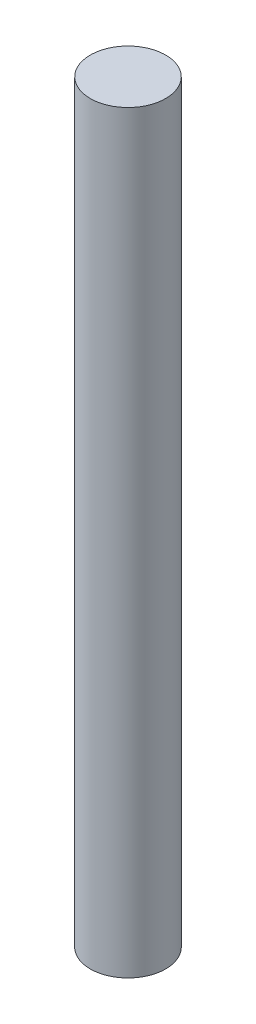
SolidWorks part; units mm, degrees
ref_plane "Plano frontal" through (0, 0, 0) normal (0, 0, 1) x (1, 0, 0)
ref_plane "Plano superior" through (0, 0, 0) normal (0, 1, 0) x (1, 0, 0)
ref_plane "Plano direito" through (0, 0, 0) normal (1, 0, 0) x (0, 0, -1)
sketch "Esboço1" plane through (0, 0, 0) normal (0, 1, 0) x (1, 0, 0)
  circle A0 centre (0, 0) radius 10
extrude "Ressalto-extrusão1" add sketch "Esboço1" along normal blind 200
